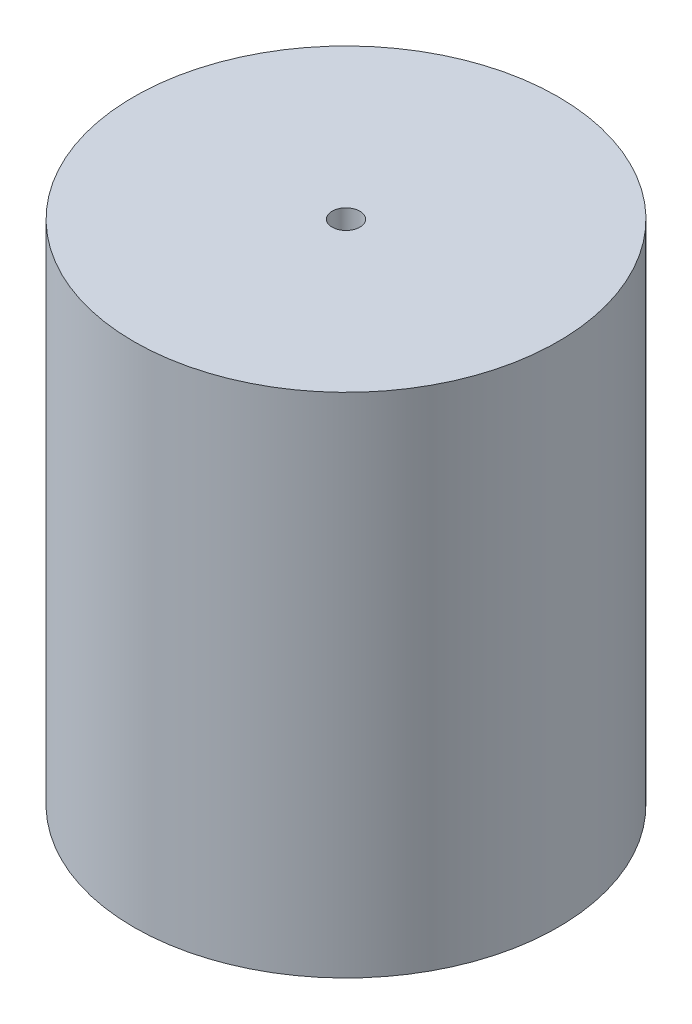
SolidWorks part; units mm, degrees
material "1060 Alloy"
ref_plane "Front Plane" through (0, 0, 0) normal (0, 0, 1) x (1, 0, 0)
ref_plane "Top Plane" through (0, 0, 0) normal (0, 1, 0) x (1, 0, 0)
ref_plane "Right Plane" through (0, 0, 0) normal (1, 0, 0) x (0, 0, -1)
sketch "Sketch1" plane through (0, 0, 0) normal (0, 1, 0) x (1, 0, 0)
  line L0 (0, 11.5) -> (0, -11.5) construction
  circle A0 centre (0, 0) radius 11.5
  dimension "D1" = 23
extrude "Boss-Extrude1" add sketch "Sketch1" along normal blind 27.5
sketch "Sketch2" plane through (0, 27.5, 0) normal (0, 1, 0) x (1, 0, 0)
  circle A0 centre (0, 0) radius 0.7525
  dimension "D1" = 1.505
extrude "Cut-Extrude1" cut sketch "Sketch2" against normal blind 5
